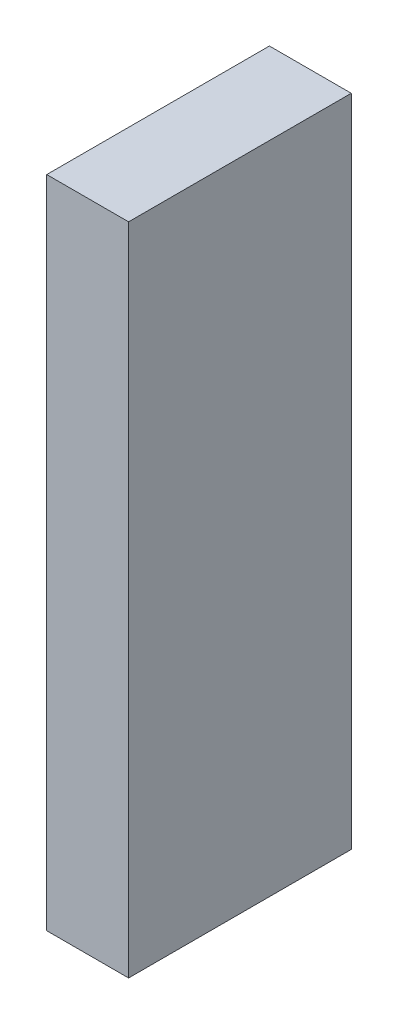
SolidWorks part; units mm, degrees
material "POLYURETHANE (11671)"
ref_plane "Front Plane" through (0, 0, 0) normal (0, 0, 1) x (1, 0, 0)
ref_plane "Top Plane" through (0, 0, 0) normal (0, 1, 0) x (1, 0, 0)
ref_plane "Right Plane" through (0, 0, 0) normal (1, 0, 0) x (0, 0, -1)
sketch "Sketch1" plane through (0, 0, 0) normal (1, 0, 0) x (0, 0, -1)
  line L1 (-4.318, -12.7) -> (4.318, -12.7)
  line L2 (-4.318, -12.7) -> (-4.318, 12.7)
  line L3 (-4.318, 12.7) -> (4.318, 12.7)
  line L4 (4.318, -12.7) -> (4.318, 12.7)
  line L5 (-4.318, -12.7) -> (4.318, 12.7) construction
  line L6 (-4.318, 12.7) -> (4.318, -12.7) construction
  point P0 (0, 0)
  dimension "D1" = 8.636
  dimension "D2" = 25.4
extrude "Boss-Extrude1" add sketch "Sketch1" along normal blind 3.175
